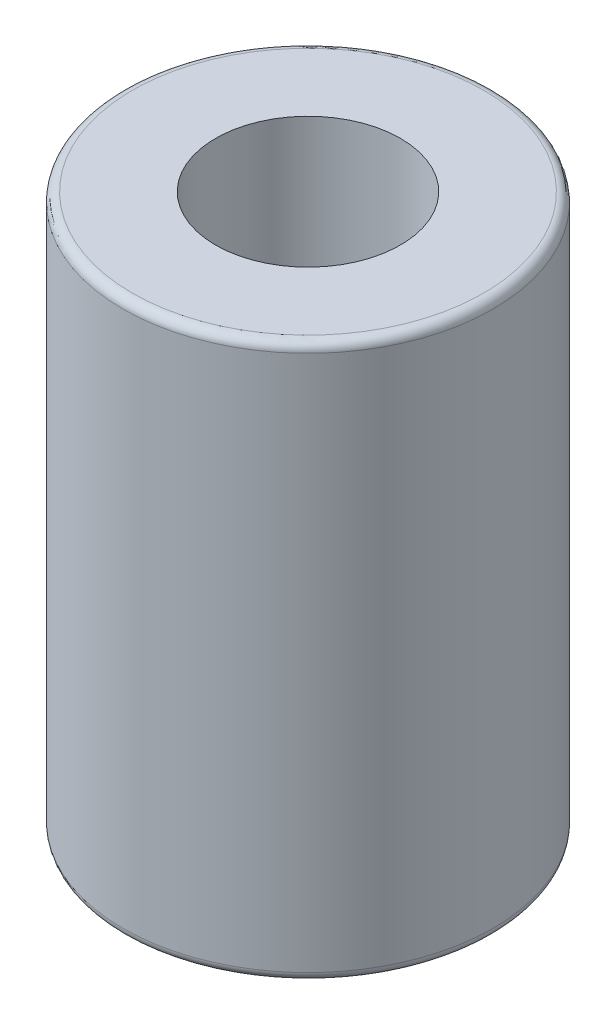
SolidWorks part; units mm, degrees
material "AISI 316 Annealed Stainless Steel Bar (SS)"
ref_plane "Front Plane" through (0, 0, 0) normal (0, 0, 1) x (1, 0, 0)
ref_plane "Top Plane" through (0, 0, 0) normal (0, 1, 0) x (1, 0, 0)
ref_plane "Right Plane" through (0, 0, 0) normal (1, 0, 0) x (0, 0, -1)
sketch "Sketch1" plane through (0, 0, 0) normal (0, 1, 0) x (1, 0, 0)
  circle A0 centre (0, 0) radius 5
  dimension "D1" = 10
extrude "Boss-Extrude1" add sketch "Sketch1" along normal blind 15
sketch "Sketch2" plane through (0, 15, 0) normal (0, 1, 0) x (1, 0, 0)
  circle A0 centre (0, 0) radius 2.5
  dimension "D1" = 5
extrude "Cut-Extrude1" cut sketch "Sketch2" against normal blind 15
fillet "Fillet1" radius 0.25 2 edges at (0, 0, 5) (0, 15, 5)
